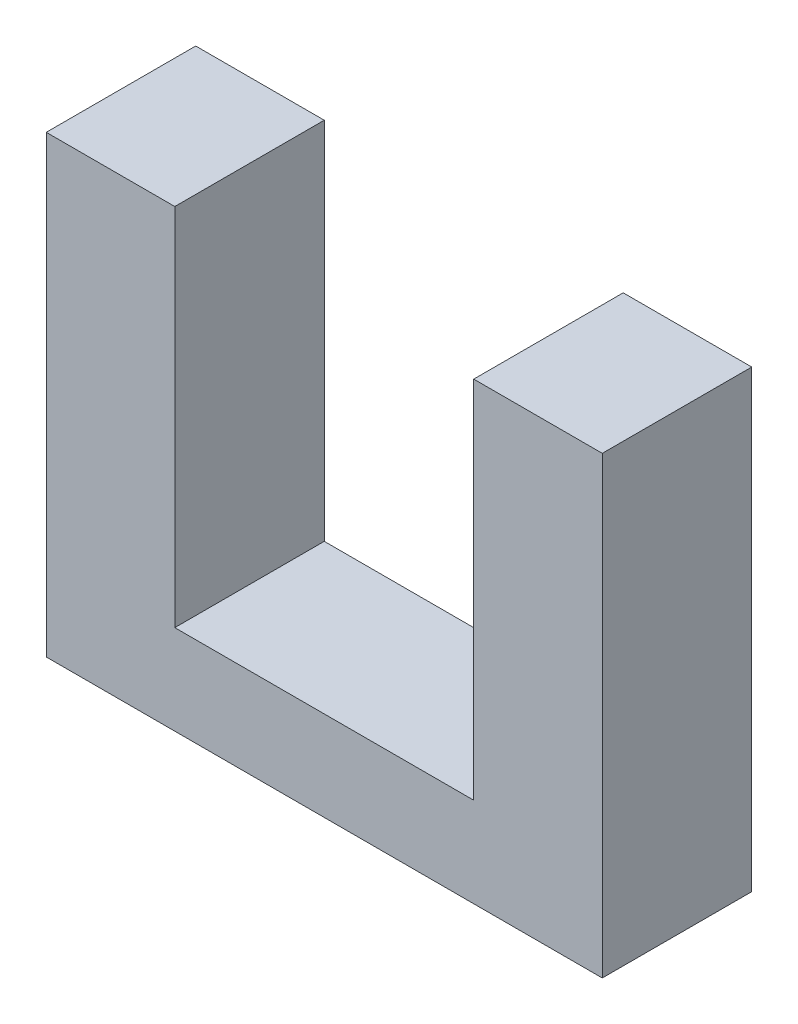
SolidWorks part; units mm, degrees
material "ABS"
ref_plane "Front Plane" through (0, 0, 0) normal (0, 0, 1) x (1, 0, 0)
ref_plane "Top Plane" through (0, 0, 0) normal (0, 1, 0) x (1, 0, 0)
ref_plane "Right Plane" through (0, 0, 0) normal (1, 0, 0) x (0, 0, -1)
sketch "Sketch1" plane through (0, 0, 0) normal (0, 0, 1) x (1, 0, 0)
  line L0 (5, 0) -> (5, 12.2)
  line L1 (-5, 0) -> (5, 0)
  line L2 (0, 0) -> (0, 18.0231) construction
  line L3 (5, 12.2) -> (9.3, 12.2)
  line L4 (9.3, 12.2) -> (9.3, -3)
  line L5 (9.3, -3) -> (-9.3, -3)
  line L6 (-9.3, 12.2) -> (-9.3, -3)
  line L7 (-5, 12.2) -> (-9.3, 12.2)
  line L8 (-5, 0) -> (-5, 12.2)
  point P9 (0, -3)
extrude "Boss-Extrude1" add sketch "Sketch1" against normal blind 5
